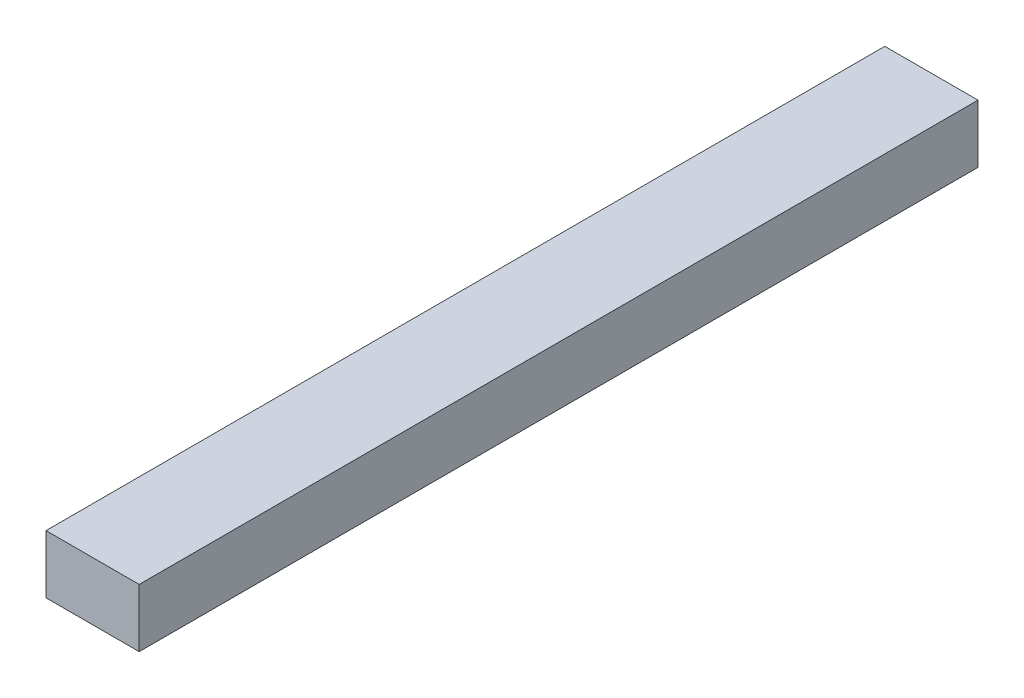
SolidWorks part; units mm, degrees
ref_plane "Front Plane" through (0, 0, 0) normal (0, 0, 1) x (1, 0, 0)
ref_plane "Top Plane" through (0, 0, 0) normal (0, 1, 0) x (1, 0, 0)
ref_plane "Right Plane" through (0, 0, 0) normal (1, 0, 0) x (0, 0, -1)
sketch "Sketch1" plane through (0, 0, 0) normal (0, 0, 1) x (1, 0, 0)
  line L1 (12.7, -7.9375) -> (-12.7, -7.9375)
  line L2 (12.7, -7.9375) -> (12.7, 7.9375)
  line L3 (12.7, 7.9375) -> (-12.7, 7.9375)
  line L4 (-12.7, -7.9375) -> (-12.7, 7.9375)
  line L5 (12.7, -7.9375) -> (-12.7, 7.9375) construction
  line L6 (12.7, 7.9375) -> (-12.7, -7.9375) construction
  point P0 (0, 0)
  dimension "D1" = 25.4
  dimension "D2" = 15.875
extrude "Boss-Extrude1" add sketch "Sketch1" along normal mid plane 228.6
hole_wizard "1/2-13 Tapped Hole1" positions "Sketch4" profile "Sketch3" tap size "1/2-13" standard "ANSI Inch"
sketch "Sketch4" plane through (0, 0, -114.3) normal (0, 0, -1) x (-1, 0, 0)
  point P0 (0, 0)
sketch "Sketch3" plane through (0, 0, -114.3) normal (1, 0, 0) x (0, 1, 0)
  line L0 (0, 0) -> (0, 31.242)
  line L1 (0, 31.242) -> (5.3581, 31.242)
  line L2 (5.3581, 31.242) -> (5.3581, 0)
  line L5 (5.3581, 0) -> (0, 0)
  line L10 (0, 31.242) -> (-5.3581, 31.242) construction
  line L11 (0, -6.35) -> (0, 107.95) construction
  dimension "Tap Drill Dia." = 10.7163
  dimension "Tap Drill Depth" = 31.242
  dimension "Drill Angle" = 180
cosmetic thread "Hole Thread1" parameters "D1"=25.4, "D2"=12.7
